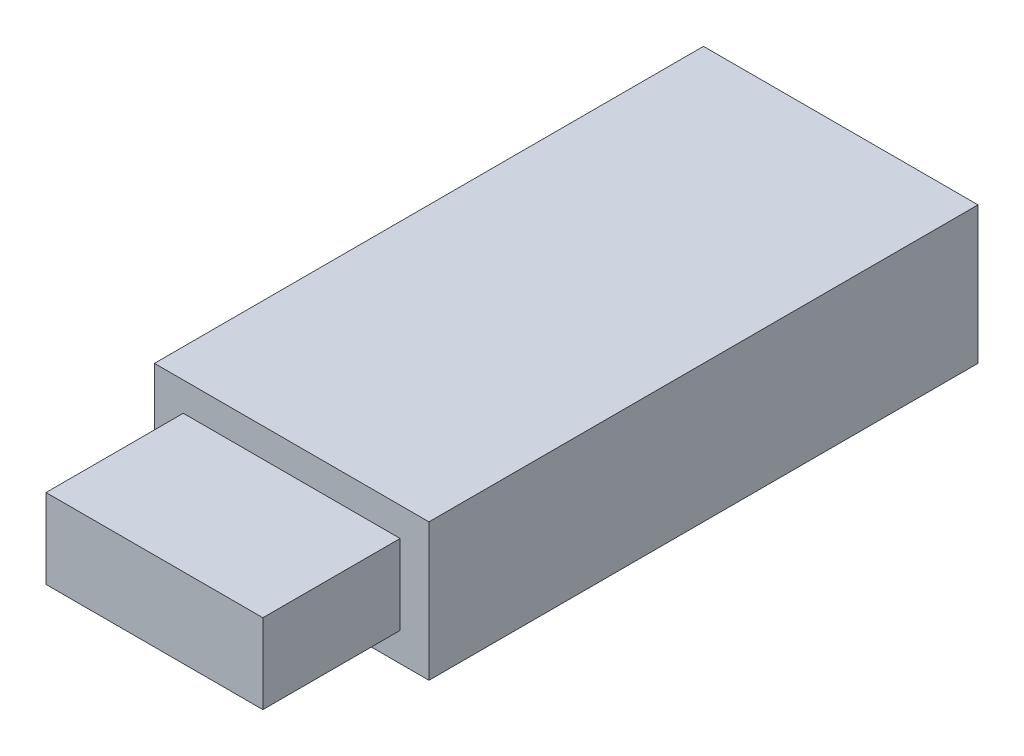
SolidWorks part; units mm, degrees
ref_plane "前视基准面" through (0, 0, 0) normal (0, 0, 1) x (1, 0, 0)
ref_plane "上视基准面" through (0, 0, 0) normal (0, 1, 0) x (1, 0, 0)
ref_plane "右视基准面" through (0, 0, 0) normal (1, 0, 0) x (0, 0, -1)
sketch "草图3" plane through (0, 0, 0) normal (0, 0, 1) x (1, 0, 0)
  line L1 (-20, 10) -> (20, 10)
  line L2 (-20, 10) -> (-20, -10)
  line L3 (-20, -10) -> (20, -10)
  line L4 (20, 10) -> (20, -10)
  dimension "D1" = 10
  dimension "D2" = 20
  dimension "D3" = 20
  dimension "D4" = 40
extrude "凸台-拉伸3" add sketch "草图3" along normal blind 100
sketch "草图4" plane through (0, 0, 100) normal (0, 0, 1) x (1, 0, 0)
  line L0 (20, -10) -> (20, 10) construction
  line L1 (-15.8, 5.8) -> (15.8, 5.8)
  line L2 (-15.8, 5.8) -> (-15.8, -5.8)
  line L3 (-15.8, -5.8) -> (15.8, -5.8)
  line L4 (15.8, 5.8) -> (15.8, -5.8)
  line L5 (-20, 10) -> (-20, -10) construction
  line L6 (20, 10) -> (-20, 10) construction
  line L7 (-20, -10) -> (20, -10) construction
  line M4 (-20, 10) -> (-20, -10)
  line M5 (-20, -10) -> (20, -10)
  line M6 (20, -10) -> (20, 10)
  line M7 (20, 10) -> (-20, 10)
  dimension "D1" = 4.2
  dimension "D2" = 4.2
  dimension "D3" = 4.2
  dimension "D4" = 4.2
extrude "切除-拉伸1" cut sketch "草图4" against normal blind 20 contours L1 L4 L3 L2 M7 M4 M5 M6
